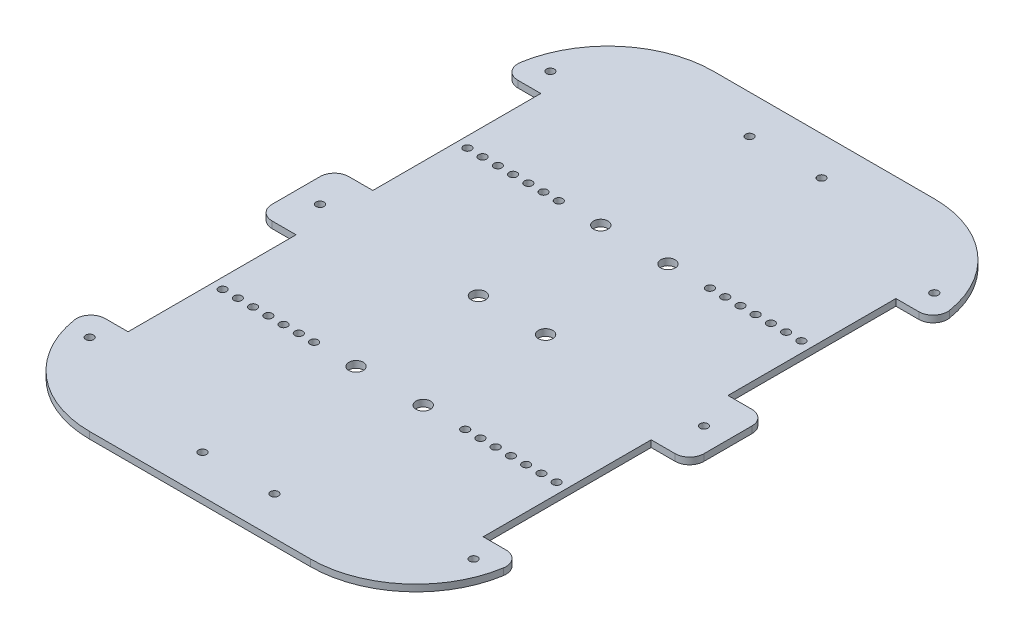
SolidWorks part; units mm, degrees
ref_plane "Ön Düzlem" through (0, 0, 0) normal (0, 0, 1) x (1, 0, 0)
ref_plane "Üst Düzlem" through (0, 0, 0) normal (0, 1, 0) x (1, 0, 0)
ref_plane "Sağ Düzlem" through (0, 0, 0) normal (1, 0, 0) x (0, 0, -1)
sketch "Sketch2" plane through (0, 0, 0) normal (0, 1, 0) x (1, 0, 0)
  line L0 (-74, -86) -> (-74, -51) construction
  line L1 (46, -130) -> (-46, -130)
  line L2 (90, -10) -> (90, 10)
  line L3 (46, 130) -> (-46, 130)
  line L4 (-90, -10) -> (-90, 10)
  line L5 (90, -130) -> (-90, 130) construction
  line L6 (90, 130) -> (-90, -130) construction
  line L7 (-83.5233, 86) -> (-74, 86)
  line L9 (-84, 16) -> (-74, 16)
  line L10 (-74, 86) -> (-74, 16)
  line L11 (-83.5233, -86) -> (-74, -86)
  line L13 (-84, -16) -> (-74, -16)
  line L14 (-74, -86) -> (-74, -16)
  line L15 (83.5233, 86) -> (74, 86)
  line L17 (84, 16) -> (74, 16)
  line L18 (74, 86) -> (74, 16)
  line L19 (83.5233, -86) -> (74, -86)
  line L21 (84, -16) -> (74, -16)
  line L22 (74, -86) -> (74, -16)
  line L23 (-74, 51) -> (74, 51) construction
  line L24 (-74, -51) -> (74, -51) construction
  arc A2 (-46, -130) -> (-89.4481, -92.9474) centre (-46, -86) cw
  arc A3 (-89.4481, 92.9474) -> (-46, 130) centre (-46, 86) cw
  arc A4 (89.4481, 92.9474) -> (46, 130) centre (46, 86) ccw
  arc A5 (89.4481, -92.9474) -> (46, -130) centre (46, -86) cw
  arc A6 (-84, 16) -> (-90, 10) centre (-84, 10) ccw
  arc A7 (-84, -16) -> (-90, -10) centre (-84, -10) cw
  arc A8 (90, 10) -> (84, 16) centre (84, 10) ccw
  arc A9 (90, -10) -> (84, -16) centre (84, -10) cw
  arc A10 (-89.4481, -92.9474) -> (-83.5233, -86) centre (-83.5233, -92) cw
  arc A11 (83.5233, -86) -> (89.4481, -92.9474) centre (83.5233, -92) cw
  arc A12 (-89.4481, 92.9474) -> (-83.5233, 86) centre (-83.5233, 92) ccw
  arc A13 (89.4481, 92.9474) -> (83.5233, 86) centre (83.5233, 92) cw
  point P0 (0, 0)
  point P34 (-90, -16)
  point P39 (90, -16)
  point P46 (-90, 86)
  point P49 (90, 86)
  dimension "D3" = 44
  dimension "D4" = 44
  dimension "D5" = 44
  dimension "D6" = 44
  dimension "D15" = 6
  dimension "D16" = 6
  dimension "D17" = 6
  dimension "D18" = 6
  dimension "D19" = 6
  dimension "D20" = 6
  dimension "D21" = 6
  dimension "D22" = 6
  dimension "D1" = 260
  dimension "D2" = 180
  dimension "D7" = 16
  dimension "D8" = 70
  dimension "D9" = 16
  dimension "D10" = 70
  dimension "D11" = 70
  dimension "D12" = 16
  dimension "D13" = 16
  dimension "D14" = 70
extrude "Boss-Extrude4" add sketch "Sketch2" along normal blind 2.8
sketch "Sketch5" plane through (0, 2.8, 0) normal (0, 1, 0) x (1, 0, 0)
  circle A0 centre (-69.6, -51) radius 1.65
  circle A1 centre (-63.25, -51) radius 1.65
  circle A2 centre (-56.9, -51) radius 1.65
  circle A3 centre (-50.55, -51) radius 1.65
  circle A4 centre (-44.2, -51) radius 1.65
  circle A5 centre (-37.85, -51) radius 1.65
  circle A6 centre (-31.5, -51) radius 1.65
  circle A7 centre (31.5, -51) radius 1.65
  circle A8 centre (37.85, -51) radius 1.65
  circle A9 centre (44.2, -51) radius 1.65
  circle A10 centre (50.55, -51) radius 1.65
  circle A11 centre (56.9, -51) radius 1.65
  circle A12 centre (63.25, -51) radius 1.65
  circle A13 centre (69.6, -51) radius 1.65
  circle A14 centre (69.6, 51) radius 1.65
  circle A15 centre (63.25, 51) radius 1.65
  circle A16 centre (56.9, 51) radius 1.65
  circle A17 centre (50.55, 51) radius 1.65
  circle A18 centre (44.2, 51) radius 1.65
  circle A19 centre (37.85, 51) radius 1.65
  circle A20 centre (31.5, 51) radius 1.65
  circle A21 centre (-31.5, 51) radius 1.65
  circle A22 centre (-37.85, 51) radius 1.65
  circle A23 centre (-44.2, 51) radius 1.65
  circle A24 centre (-50.55, 51) radius 1.65
  circle A25 centre (-56.9, 51) radius 1.65
  circle A26 centre (-63.25, 51) radius 1.65
  circle A27 centre (-69.6, 51) radius 1.65
  circle A29 centre (-14, -51) radius 3
  circle A30 centre (14, -51) radius 3
  circle A31 centre (14, 51) radius 3
  circle A32 centre (-14, 51) radius 3
  circle A33 centre (-14, 0) radius 3
  circle A34 centre (14, 0) radius 3
  circle A35 centre (-80, 96) radius 1.65
  circle A36 centre (-80, 0) radius 1.65
  circle A37 centre (80, 0) radius 1.65
  circle A38 centre (-80, -96) radius 1.65
  circle A39 centre (80, -96) radius 1.65
  circle A40 centre (80, 96) radius 1.65
  circle A41 centre (-15, -114) radius 1.65
  circle A42 centre (15, -114) radius 1.65
  circle A43 centre (15, 114) radius 1.65
  circle A44 centre (-15, 114) radius 1.65
extrude "Cut-Extrude1" cut sketch "Sketch5" against normal through all
